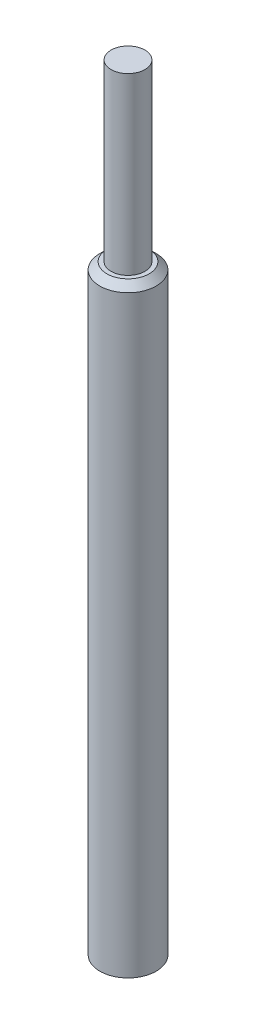
SolidWorks part; units mm, degrees
ref_plane "Front Plane" through (0, 0, 0) normal (0, 0, 1) x (1, 0, 0)
ref_plane "Top Plane" through (0, 0, 0) normal (0, 1, 0) x (1, 0, 0)
ref_plane "Right Plane" through (0, 0, 0) normal (1, 0, 0) x (0, 0, -1)
sketch "Sketch1" plane through (0, 0, 0) normal (0, 0, 1) x (1, 0, 0)
  line L0 (0, 61.6791) -> (0, -84.7656) construction
  line L1 (0, -79.597) -> (10, -79.597)
  line L2 (10, -79.597) -> (10, 133.403)
  line L3 (0, 61.6791) -> (0, 225.7467) construction
  line L4 (0, 195.403) -> (0, -79.597)
  line L5 (0, 195.403) -> (6, 195.403)
  line L6 (6, 195.403) -> (6, 133.403)
  line L7 (6, 133.403) -> (10, 133.403)
revolve "Revolve1" add sketch "Sketch1" angle 360 about L3
chamfer "Chamfer1" distance 2.5 angle 45 1 edges at (0, 133.403, -10)
